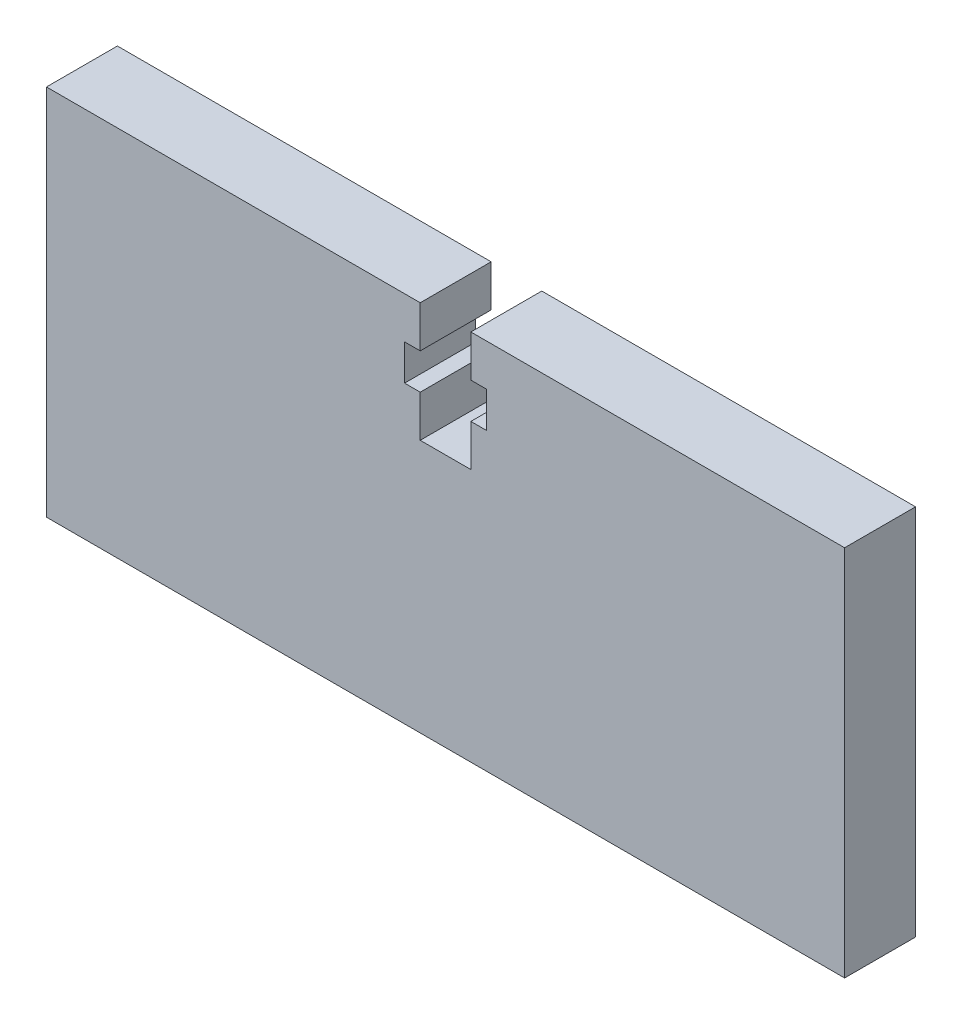
SolidWorks part; units mm, degrees
ref_plane "Front Plane" through (0, 0, 0) normal (0, 0, 1) x (1, 0, 0)
ref_plane "Top Plane" through (0, 0, 0) normal (0, 1, 0) x (1, 0, 0)
ref_plane "Right Plane" through (0, 0, 0) normal (1, 0, 0) x (0, 0, -1)
sketch "Sketch1" plane through (0, 0, 0) normal (0, 0, 1) x (1, 0, 0)
  line L0 (0, 16.51) -> (0, -7.29) construction
  line L2 (-26.797, -8.51) -> (-26.797, 16.51)
  line L3 (-26.797, 16.51) -> (-1.7, 16.51)
  line L4 (26.797, -8.51) -> (26.797, 16.51)
  line L5 (-26.797, -16.51) -> (26.797, 16.51) construction
  line L6 (-26.797, 16.51) -> (26.797, -16.51) construction
  line L7 (-13.4509, -7.29) -> (13.4509, -7.29) construction
  line L8 (0, 5.91) -> (26.797, 5.91) construction
  line L9 (-1.7, 16.51) -> (-1.7, 13.71)
  line L10 (-1.7, 13.71) -> (-2.75, 13.71)
  line L11 (-2.75, 13.71) -> (-2.75, 11.31)
  line L12 (-2.75, 11.31) -> (-1.7, 11.31)
  line L13 (-1.7, 11.31) -> (-1.7, 8.51)
  line L14 (-1.7, 8.51) -> (1.7, 8.51)
  line L15 (-2.75, 12.51) -> (0, 12.51) construction
  line L16 (1.7, 11.31) -> (1.7, 8.51)
  line L17 (2.75, 11.31) -> (1.7, 11.31)
  line L18 (2.75, 13.71) -> (2.75, 11.31)
  line L19 (1.7, 13.71) -> (2.75, 13.71)
  line L20 (1.7, 16.51) -> (1.7, 13.71)
  line L21 (1.7, 16.51) -> (26.797, 16.51)
  line L22 (0, 0) -> (26.797, 0) construction
  line L34 (-26.797, -8.51) -> (26.797, -8.51)
  point P0 (0, 0)
  point P23 (0, 8.51)
  dimension "D1" = 33.02
  dimension "D2" = 53.594
  dimension "D3" = 1.7
  dimension "D4" = 2.75
  dimension "D5" = 8
  dimension "D6" = 4
  dimension "D7" = 2.4
extrude "Boss-Extrude1" add sketch "Sketch1" along normal blind 4.7625
equation "\"D6@Sketch1\"=\"D5@Sketch1\"/2"
